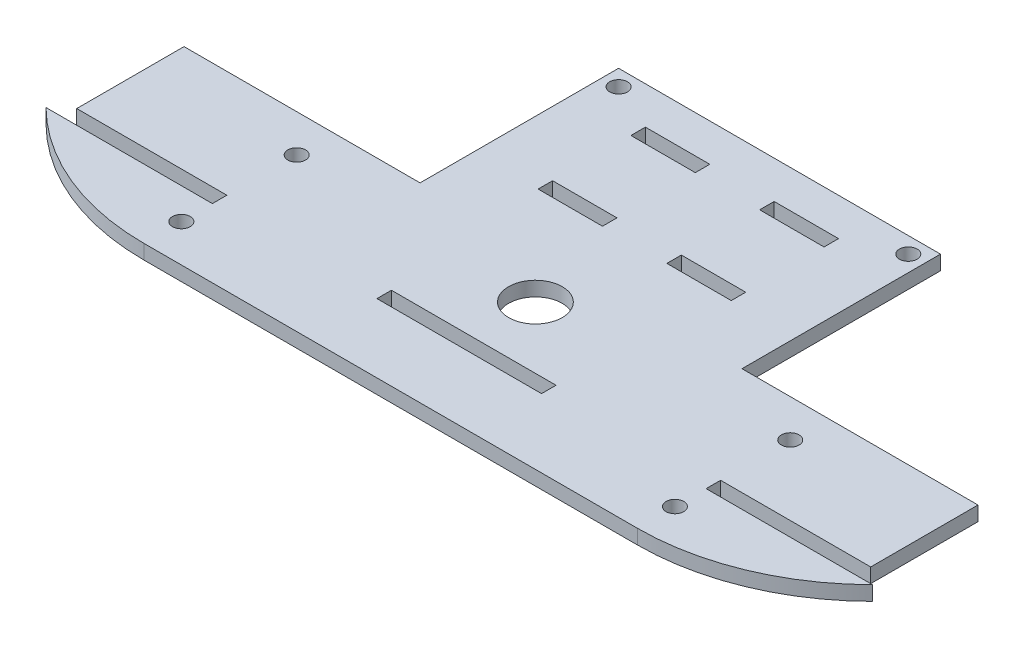
SolidWorks part; units mm, degrees
ref_plane "Ön Düzlem" through (0, 0, 0) normal (0, 0, 1) x (1, 0, 0)
ref_plane "Üst Düzlem" through (0, 0, 0) normal (0, 1, 0) x (1, 0, 0)
ref_plane "Sağ Düzlem" through (0, 0, 0) normal (1, 0, 0) x (0, 0, -1)
sketch "Sketch1" plane through (0, 0, 0) normal (0, 1, 0) x (1, 0, 0)
  line L1 (-46, 0) -> (46, 0)
  line L19 (-73.9952, 35.5) -> (-73.9952, 15.5)
  line L21 (73.9952, 35.5) -> (73.9952, 15.5)
  line L22 (-15.34, 15.5) -> (-15.34, 12.8)
  line L23 (-46.0152, 15.5) -> (-46.0152, 12.8)
  line L24 (-15.34, 12.8) -> (15.34, 12.8)
  line L25 (15.34, 12.8) -> (15.34, 15.5)
  line L26 (15.34, 15.5) -> (-15.34, 15.5)
  line L29 (46.0152, 15.5) -> (46.0152, 12.8)
  line L31 (46.0152, 15.5) -> (73.9952, 15.5)
  line L32 (77.0252, 12.8) -> (46.0152, 12.8)
  line L33 (-46.0152, 15.5) -> (-73.9952, 15.5)
  line L34 (-46.0152, 12.8) -> (-77.0252, 12.8)
  line L55 (-30, 70.5) -> (-30, 72.5)
  line L56 (73.9952, 35.5) -> (30, 35.5)
  line L57 (18, 45.5) -> (6, 45.5)
  line L59 (-6, 62.8) -> (-18, 62.8)
  line L60 (6, 45.5) -> (6, 48.2)
  line L61 (18, 62.8) -> (6, 62.8)
  line L63 (-6, 65.5) -> (-6, 62.8)
  line L64 (-6, 65.5) -> (-18, 65.5)
  line L65 (-6, 48.2) -> (-18, 48.2)
  line L66 (18, 65.5) -> (6, 65.5)
  line L67 (-6, 45.5) -> (-18, 45.5)
  line L68 (18, 48.2) -> (6, 48.2)
  line L71 (-18, 45.5) -> (-18, 48.2)
  line L72 (6, 65.5) -> (6, 62.8)
  line L73 (-18, 65.5) -> (-18, 62.8)
  line L74 (-6, 45.5) -> (-6, 48.2)
  line L75 (30, 70.5) -> (30, 35.5)
  line L76 (-30, 35.5) -> (-30, 70.5)
  line L77 (18, 45.5) -> (18, 48.2)
  line L78 (18, 65.5) -> (18, 62.8)
  line L79 (-30, 35.5) -> (-73.9952, 35.5)
  line L81 (-30, 72.5) -> (30, 72.5)
  line L82 (30, 72.5) -> (30, 70.5)
  arc A0 (-77.0252, 12.8) -> (-46, 0) centre (-46, 44) ccw
  arc A1 (46, 0) -> (77.0252, 12.8) centre (46, 44) ccw
  circle A2 centre (46, 28.5) radius 1.65
  circle A3 centre (46, 7) radius 1.65
  circle A4 centre (-46, 7) radius 1.65
  circle A5 centre (-46, 28.5) radius 1.65
  circle A6 centre (-27, 69.5) radius 1.65
  circle A7 centre (27, 69.5) radius 1.65
  circle A8 centre (0, 27) radius 5
  point P52 (0, 50.5)
extrude "Boss-Extrude1" add sketch "Sketch1" along normal blind 2.7
